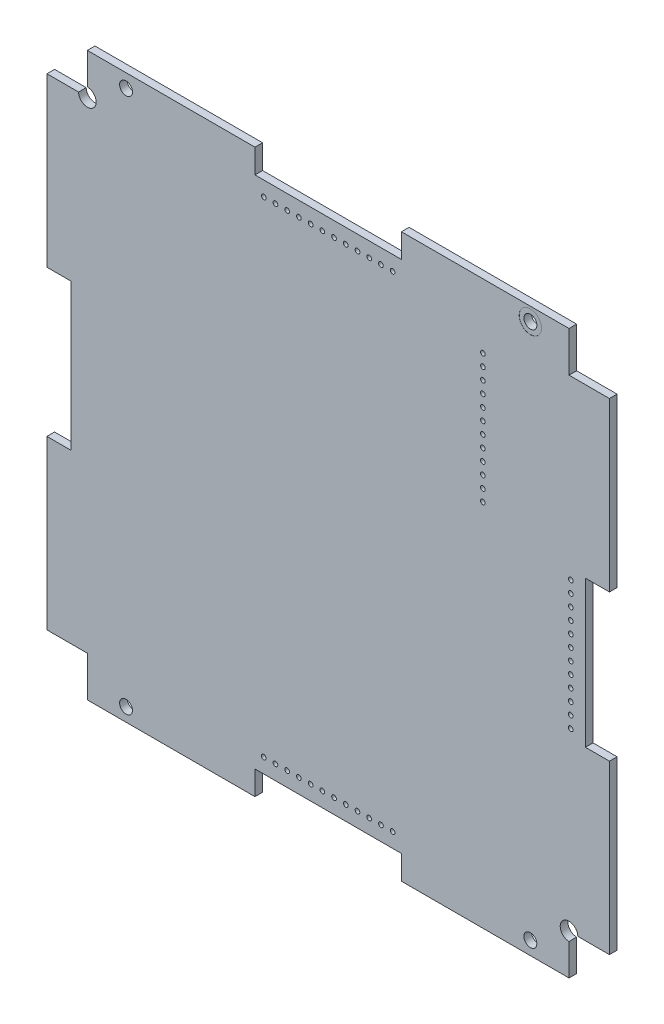
SolidWorks part; units mm, degrees
material "電力回路基板"
ref_plane "正面" through (0, 0, 0) normal (0, 0, 1) x (1, 0, 0)
ref_plane "平面" through (0, 0, 0) normal (0, 1, 0) x (1, 0, 0)
ref_plane "右側面" through (0, 0, 0) normal (1, 0, 0) x (0, 0, -1)
sketch "Sketch1" plane through (0, 0, 0) normal (0, 0, 1) x (1, 0, 0)
  line L0 (-48.1, 12.5) -> (-43.9, 12.5)
  line L1 (-48.1, 48.1) -> (-12.5, 48.1)
  line L2 (-48.1, 48.1) -> (-48.1, 12.5)
  line L3 (-48.1, -48.1) -> (-12.5, -48.1)
  line L4 (48.1, 48.1) -> (48.1, 12.5)
  line L5 (-48.1, 48.1) -> (48.1, -48.1) construction
  line L6 (-48.1, -48.1) -> (48.1, 48.1) construction
  line L7 (-43.9, 12.5) -> (-43.9, -12.5)
  line L8 (-43.9, -12.5) -> (-48.1, -12.5)
  line L9 (43.9, 12.5) -> (43.9, -12.5)
  line L10 (43.9, -12.5) -> (48.1, -12.5)
  line L11 (43.9, 12.5) -> (48.1, 12.5)
  line L12 (-12.5, -48.1) -> (-12.5, -43.9)
  line L13 (-12.5, -43.9) -> (12.5, -43.9)
  line L14 (12.5, -43.9) -> (12.5, -48.1)
  line L15 (-12.5, 48.1) -> (-12.5, 43.9)
  line L16 (-12.5, 43.9) -> (12.5, 43.9)
  line L17 (12.5, 43.9) -> (12.5, 48.1)
  line L18 (-48.1, -12.5) -> (-48.1, -48.1)
  line L19 (48.1, -12.5) -> (48.1, -48.1)
  line L20 (12.5, -48.1) -> (48.1, -48.1)
  line L21 (12.5, 48.1) -> (48.1, 48.1)
  point P0 (0, 0)
  dimension "D1" = 96.2
  dimension "D2" = 96.2
  dimension "D3" = 25
  dimension "D4" = 4.2
  dimension "D5" = 35.6
  dimension "D6" = 35.6
  dimension "D7" = 35.6
  dimension "D8" = 35.6
extrude "Boss-Extrude1" add sketch "Sketch1" along normal blind 1.3
sketch "Sketch2" plane through (0, 0, 1.3) normal (0, 0, 1) x (1, 0, 0)
  line L0 (48.1, -48.1) -> (48.1, -12.5) construction
  line L1 (-41.1, 41.1) -> (-48.1, 41.1)
  line L2 (-41.1, 41.1) -> (-41.1, 48.1)
  line L3 (-41.1, 48.1) -> (-48.1, 48.1)
  line L4 (-48.1, 41.1) -> (-48.1, 48.1)
  line L5 (48.1, 48.1) -> (41.1, 48.1)
  line L6 (48.1, 48.1) -> (48.1, 41.1)
  line L7 (48.1, 41.1) -> (41.1, 41.1)
  line L8 (41.1, 48.1) -> (41.1, 41.1)
  line L9 (48.1, -41.1) -> (41.1, -41.1)
  line L10 (48.1, -41.1) -> (48.1, -48.1)
  line L11 (48.1, -48.1) -> (41.1, -48.1)
  line L12 (41.1, -41.1) -> (41.1, -48.1)
  line L13 (12.5, -48.1) -> (48.1, -48.1) construction
  line L15 (-48.1, -48.1) -> (-41.1, -48.1)
  line L16 (-48.1, -48.1) -> (-48.1, -41.1)
  line L17 (-48.1, -41.1) -> (-41.1, -41.1)
  line L18 (-41.1, -48.1) -> (-41.1, -41.1)
  dimension "D1" = 7
extrude "Cut-Extrude1" cut sketch "Sketch2" against normal blind 8.5
sketch "Sketch15" plane through (0, 0, 1.3) normal (0, 0, 1) x (1, 0, 0)
  line L0 (-12.5, 48.1) -> (-41.1, 48.1) construction
  line L1 (-41.1, 41.1) -> (-41.1, 48.1) construction
  line L2 (41.1, 48.1) -> (12.5, 48.1) construction
  line L3 (41.1, 48.1) -> (41.1, 41.1) construction
  line L4 (-41.1, -48.1) -> (-12.5, -48.1) construction
  line L5 (-41.1, -48.1) -> (-41.1, -41.1) construction
  line L6 (12.5, -48.1) -> (41.1, -48.1) construction
  line L7 (41.1, -41.1) -> (41.1, -48.1) construction
  point P0 (-34.5, 45.7)
  point P1 (34.5, 45.7)
  point P2 (-34.5, -45.7)
  point P3 (34.5, -45.7)
  dimension "D1" = 2.4
  dimension "D2" = 6.6
  dimension "D3" = 2.4
  dimension "D4" = 6.6
  dimension "D5" = 2.4
  dimension "D6" = 6.6
  dimension "D7" = 2.4
  dimension "D8" = 6.6
hole_wizard "Ø2.2 (2.2) Diameter Hole1" positions "Sketch17" profile "Sketch16" hole size "Ø2.2" standard "ANSI Metric"
sketch "Sketch17" plane through (0, 0, 1.3) normal (0, 0, 1) x (1, 0, 0)
  point P0 (-34.5, 45.7)
  point P3 (34.5, 45.7)
  point P6 (-34.5, -45.7)
  point P9 (34.5, -45.7)
sketch "Sketch16" plane through (-34.5, 45.7, 1.3) normal (1, 0, 0) x (0, -1, 0)
  line L0 (0, 0) -> (0, 13)
  line L1 (0, 13) -> (1.1, 13)
  line L2 (1.1, 13) -> (1.1, 0)
  line L5 (1.1, 0) -> (0, 0)
  line L10 (0, 13) -> (-1.1, 13) construction
  line L11 (0, -6.35) -> (0, 107.95) construction
  dimension "Hole Dia." = 2.2
  dimension "Hole Depth" = 13
  dimension "Drill Angle" = 180
sketch "Sketch18" plane through (0, 0, 0) normal (0, 0, -1) x (-1, 0, 0)
  circle A0 centre (41.1, 41.1) radius 1.5
  circle A1 centre (-41.1, -41.1) radius 1.5
  dimension "D1" = 3
  dimension "D2" = 3
extrude "Cut-Extrude2" cut sketch "Sketch18" against normal through all
sketch "Sketch19" plane through (0, 0, 0) normal (0, 0, -1) x (-1, 0, 0)
  line L0 (48.1, -41.1) -> (41.1, -41.1) construction
  line L1 (48.1, 41.1) -> (48, 41.1)
  line L2 (48.1, 41.1) -> (48.1, -41.1)
  line L3 (48.1, -41.1) -> (48, -41.1)
  line L4 (48, 41.1) -> (48, -41.1)
  line L5 (-41.1, -48.1) -> (-41.1, -42.6) construction
  line L6 (41.1, -48.1) -> (-41.1, -48.1)
  line L7 (41.1, -48.1) -> (41.1, -48)
  line L8 (41.1, -48) -> (-41.1, -48)
  line L9 (-41.1, -48.1) -> (-41.1, -48)
  line L10 (-48.1, 41.1) -> (-41.1, 41.1) construction
  line L11 (-48.1, -41.1) -> (-48, -41.1)
  line L12 (-48.1, -41.1) -> (-48.1, 41.1)
  line L13 (-48.1, 41.1) -> (-48, 41.1)
  line L14 (-48, -41.1) -> (-48, 41.1)
  line L15 (41.1, 48.1) -> (41.1, 42.6) construction
  line L16 (-41.1, 48.1) -> (41.1, 48.1)
  line L17 (-41.1, 48.1) -> (-41.1, 48)
  line L18 (-41.1, 48) -> (41.1, 48)
  line L19 (41.1, 48.1) -> (41.1, 48)
  dimension "D1" = 0.1
  dimension "D2" = 0.1
  dimension "D3" = 0.1
  dimension "D4" = 0.1
extrude "Cut-Extrude3" cut sketch "Sketch19" against normal through all
sketch "Sketch20" plane through (0, 0, 1.3) normal (0, 0, 1) x (1, 0, 0)
  line L2 (-48, -12.5) -> (-48, -41.1) construction
  line L3 (-41.1, -48) -> (-12.5, -48) construction
  circle A0 centre (26.4, 15) radius 0.4
  circle A1 centre (26.4, 17) radius 0.4
  circle A2 centre (26.4, 19) radius 0.4
  circle A3 centre (26.4, 21) radius 0.4
  circle A4 centre (26.4, 23) radius 0.4
  circle A5 centre (26.4, 25) radius 0.4
  circle A6 centre (26.4, 27) radius 0.4
  circle A7 centre (26.4, 29) radius 0.4
  circle A8 centre (26.4, 31) radius 0.4
  circle A9 centre (26.4, 33) radius 0.4
  circle A10 centre (26.4, 35) radius 0.4
  circle A11 centre (26.4, 37) radius 0.4
  dimension "D1" = 74.4
  dimension "D2" = 63
  dimension "D3" = 12
extrude "Cut-Extrude4" cut sketch "Sketch20" against normal up to next
sketch "Sketch21" plane through (0, 0, 1.3) normal (0, 0, 1) x (1, 0, 0)
  line L0 (12.5, 43.9) -> (-12.5, 43.9) construction
  line L1 (48, 12.5) -> (48, 41.1) construction
  circle A0 centre (11, 41.4) radius 0.4
  circle A1 centre (9, 41.4) radius 0.4
  circle A2 centre (7, 41.4) radius 0.4
  circle A3 centre (5, 41.4) radius 0.4
  circle A4 centre (3, 41.4) radius 0.4
  circle A5 centre (1, 41.4) radius 0.4
  circle A6 centre (-1, 41.4) radius 0.4
  circle A7 centre (-3, 41.4) radius 0.4
  circle A8 centre (-5, 41.4) radius 0.4
  circle A9 centre (-7, 41.4) radius 0.4
  circle A10 centre (-9, 41.4) radius 0.4
  circle A11 centre (-11, 41.4) radius 0.4
  dimension "D1" = 0.8
  dimension "D2" = 2.5
  dimension "D3" = 37
  dimension "D4" = 12
extrude "Cut-Extrude5" cut sketch "Sketch21" against normal through all
sketch "Sketch22" plane through (0, 0, 1.3) normal (0, 0, 1) x (1, 0, 0)
  line L0 (41.1, 48) -> (12.5, 48) construction
  line L1 (43.9, -12.5) -> (43.9, 12.5) construction
  circle A0 centre (41.4, 11) radius 0.4
  circle A1 centre (41.4, 9) radius 0.4
  circle A2 centre (41.4, 7) radius 0.4
  circle A3 centre (41.4, 5) radius 0.4
  circle A4 centre (41.4, 3) radius 0.4
  circle A5 centre (41.4, 1) radius 0.4
  circle A6 centre (41.4, -1) radius 0.4
  circle A7 centre (41.4, -3) radius 0.4
  circle A8 centre (41.4, -5) radius 0.4
  circle A9 centre (41.4, -7) radius 0.4
  circle A10 centre (41.4, -9) radius 0.4
  circle A11 centre (41.4, -11) radius 0.4
  dimension "D1" = 0.8
  dimension "D2" = 37
  dimension "D3" = 2.5
  dimension "D4" = 12
extrude "Cut-Extrude6" cut sketch "Sketch22" against normal through all
sketch "Sketch23" plane through (0, 0, 1.3) normal (0, 0, 1) x (1, 0, 0)
  line L0 (-12.5, -43.9) -> (12.5, -43.9) construction
  line L1 (48, -41.1) -> (48, -12.5) construction
  circle A0 centre (11, -41.4) radius 0.4
  circle A1 centre (9, -41.4) radius 0.4
  circle A2 centre (7, -41.4) radius 0.4
  circle A3 centre (5, -41.4) radius 0.4
  circle A4 centre (3, -41.4) radius 0.4
  circle A5 centre (1, -41.4) radius 0.4
  circle A6 centre (-1, -41.4) radius 0.4
  circle A7 centre (-3, -41.4) radius 0.4
  circle A8 centre (-5, -41.4) radius 0.4
  circle A9 centre (-7, -41.4) radius 0.4
  circle A10 centre (-9, -41.4) radius 0.4
  circle A11 centre (-11, -41.4) radius 0.4
  dimension "D1" = 0.8
  dimension "D2" = 2.5
  dimension "D3" = 37
  dimension "D4" = 12
extrude "Cut-Extrude7" cut sketch "Sketch23" against normal through all
sketch "ｽｹｯﾁ1" plane through (0, 0, 1.3) normal (0, 0, 1) x (1, 0, 0)
  circle A1 centre (34.5, 45.7) radius 1.9
extrude "ｶｯﾄ - 押し出し1" cut sketch "ｽｹｯﾁ1" against normal blind 0.01
sketch "ｽｹｯﾁ2" plane through (0, 0, 0) normal (0, 0, -1) x (-1, 0, 0)
  circle A0 centre (-34.5, 45.7) radius 1.9
extrude "ｶｯﾄ - 押し出し2" cut sketch "ｽｹｯﾁ2" against normal blind 0.01
ref_point "点1"
ref_point "点2"
